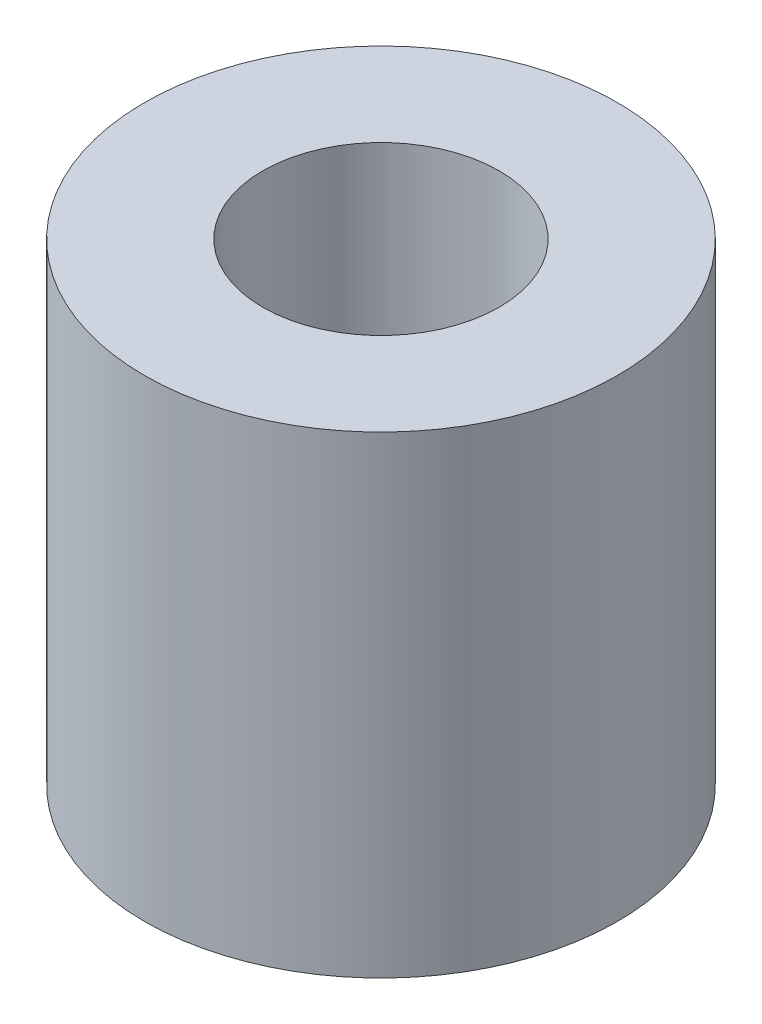
SolidWorks part; units mm, degrees
ref_plane "Front Plane" through (0, 0, 0) normal (0, 0, 1) x (1, 0, 0)
ref_plane "Top Plane" through (0, 0, 0) normal (0, 1, 0) x (1, 0, 0)
ref_plane "Right Plane" through (0, 0, 0) normal (1, 0, 0) x (0, 0, -1)
sketch "Sketch1" plane through (0, 0, 0) normal (0, 1, 0) x (1, 0, 0)
  circle A0 centre (0, 0) radius 1.5875
  circle A1 centre (0, 0) radius 3.175
  dimension "D1" = 3.175
  dimension "D2" = 6.35
extrude "Boss-Extrude1" add sketch "Sketch1" along normal blind 6.35
